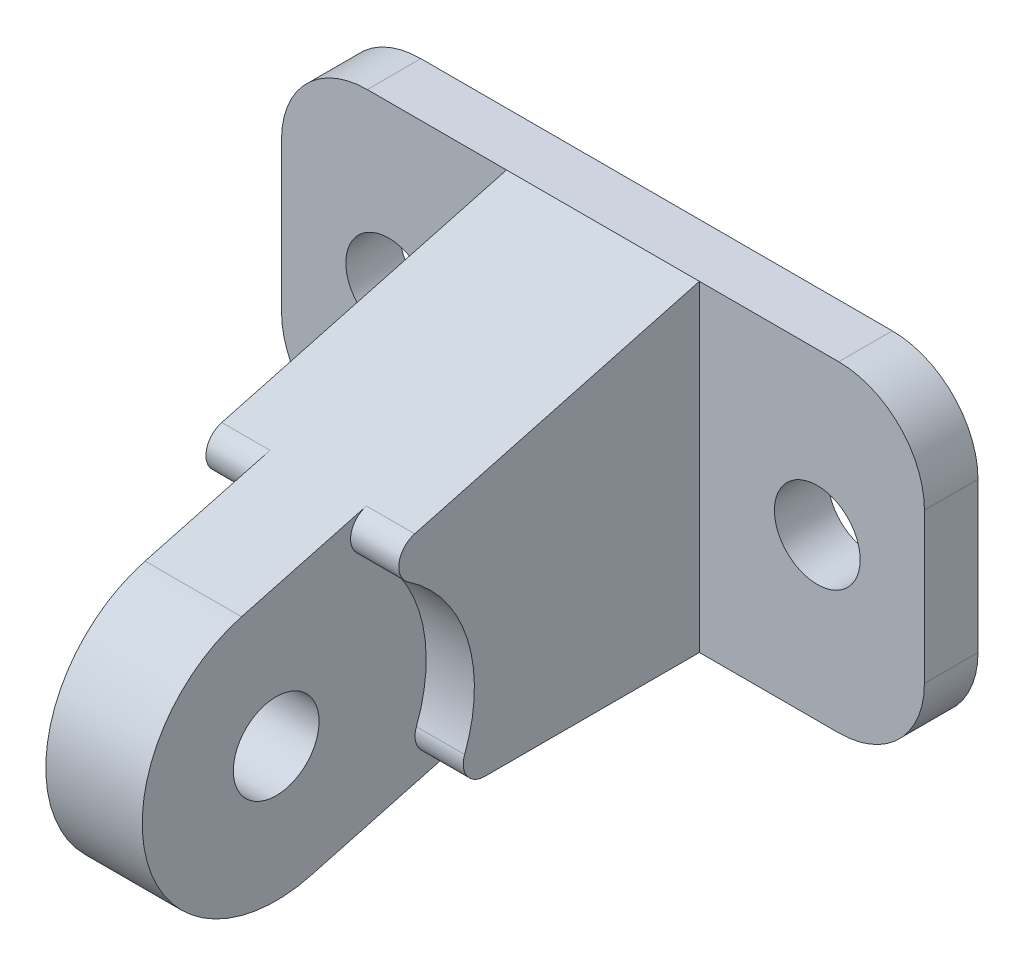
SolidWorks part; units mm, degrees
ref_plane "Front Plane" through (0, 0, 0) normal (0, 0, 1) x (1, 0, 0)
ref_plane "Top Plane" through (0, 0, 0) normal (0, 1, 0) x (1, 0, 0)
ref_plane "Right Plane" through (0, 0, 0) normal (1, 0, 0) x (0, 0, -1)
sketch "Sketch2" plane through (0, 0, 0) normal (0, 0, 1) x (1, 0, 0)
  line L1 (-22, 15) -> (22, 15)
  line L2 (-30, 7) -> (-30, -7)
  line L3 (-22, -15) -> (22, -15)
  line L4 (30, 7) -> (30, -7)
  line L5 (-30, 15) -> (-26.8, 13.4) construction
  line L6 (-30, -15) -> (-26.8, -13.4) construction
  line L7 (26.8, 13.4) -> (30, 15) construction
  line L9 (26.8, -13.4) -> (30, -15) construction
  arc A0 (22, 15) -> (30, 7) centre (22, 7) cw
  arc A1 (-30, -7) -> (-22, -15) centre (-22, -7) ccw
  arc A2 (-22, 15) -> (-30, 7) centre (-22, 7) ccw
  arc A3 (22, -15) -> (30, -7) centre (22, -7) ccw
  circle A4 centre (-20, 0) radius 4
  circle A5 centre (20, 0) radius 4
  point P0 (0, 0)
  dimension "D3" = 8
  dimension "D4" = 8
  dimension "D5" = 8
  dimension "D1" = 30
  dimension "D2" = 60
  dimension "D6" = 20
  dimension "D7" = 20
extrude "Boss-Extrude1" add sketch "Sketch2" along normal blind 5
sketch "Sketch3" plane through (0, 0, 0) normal (1, 0, 0) x (0, 0, -1)
  line L0 (-36.7648, -19.3932) -> (-5, -10.8819)
  line L1 (-5, 15) -> (-43.2352, 4.7549)
  line L2 (-5, -7) -> (-5, 7) construction
  line L3 (-5, 15) -> (-5, -10.8819)
  arc A0 (-43.2352, 4.7549) -> (-36.7648, -19.3932) centre (-40, -7.3192) ccw
  circle A1 centre (-40, -7.3192) radius 4
  dimension "D1" = 40
  dimension "D2" = 25
  dimension "D4" = 8
  dimension "D3" = 38.2352
extrude "Boss-Extrude2" add sketch "Sketch3" along normal blind 4.5 and the other way blind 4.5
ref_plane "Plane1" through (4.5, 0, 0) normal (1, 0, 0) x (0, 0, -1)
sketch "Sketch4" plane through (4.5, 0, 0) normal (1, 0, 0) x (0, 0, -1)
  line L0 (-5, -15) -> (-25.0425, -15)
  line L1 (-5, 15) -> (-31.5739, 7.8795)
  line L3 (-5, 15) -> (-5, -15)
  line L4 (-5, 15) -> (-50.0115, 15)
  arc A0 (-26.9121, -12.2899) -> (-32.1742, 4.2893) centre (-40, -7.3192) ccw
  arc A3 (-32.1742, 4.2893) -> (-31.5739, 7.8795) centre (-31.0563, 5.9477) cw
  arc A4 (-26.9121, -12.2899) -> (-25.0425, -15) centre (-25.0425, -13) ccw
  point P1 (0, 0)
  point P6 (-29.2578, -16.2973)
  point P10 (-40, -7.3192)
  point P11 (-27.219, -13)
  point P12 (-39.089, 6.6512)
  point P16 (-39.089, 5.8665)
  point P17 (-30.3339, -15)
  dimension "D1" = 28
  dimension "D2" = 2
  dimension "D3" = 15
extrude "Boss-Extrude3" add sketch "Sketch4" along normal blind 4.5 and the other way blind 13.5
